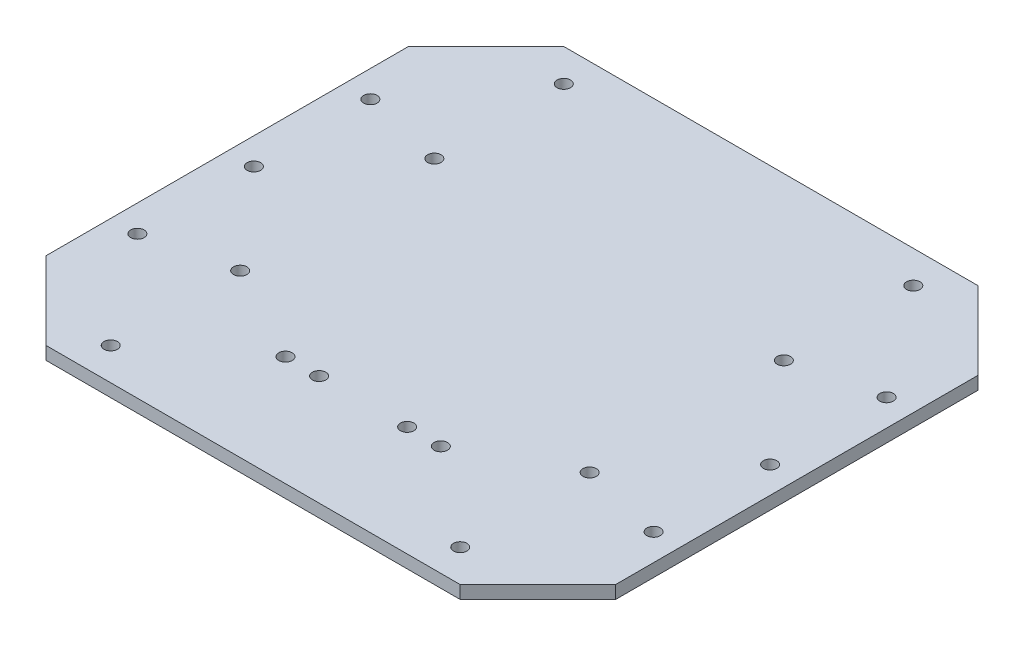
SolidWorks part; units mm, degrees
ref_plane "Front Plane" through (0, 0, 0) normal (0, 0, 1) x (1, 0, 0)
ref_plane "Top Plane" through (0, 0, 0) normal (0, 1, 0) x (1, 0, 0)
ref_plane "Right Plane" through (0, 0, 0) normal (1, 0, 0) x (0, 0, -1)
sketch "Sketch2" plane through (0, 0, 0) normal (0, 1, 0) x (1, 0, 0)
  line L0 (0, 88.9) -> (0, -88.9) construction
  line L1 (-139.7, -88.9) -> (139.7, -88.9) construction
  line L2 (-139.7, -88.9) -> (-139.7, 88.9)
  line L3 (-139.7, 88.9) -> (139.7, 88.9) construction
  line L4 (139.7, -88.9) -> (139.7, 88.9)
  line L5 (-139.7, 0) -> (139.7, 0) construction
  line L6 (-139.7, 88.9) -> (-101.6, 127)
  line L7 (-101.6, 127) -> (101.6, 127)
  line L8 (101.6, 127) -> (139.7, 88.9)
  line L9 (101.6, -127) -> (139.7, -88.9)
  line L10 (-101.6, -127) -> (101.6, -127)
  line L11 (-139.7, -88.9) -> (-101.6, -127)
  circle A11 centre (-21.59, -73.025) radius 3.302
  circle A18 centre (-38.1, -73.025) radius 3.302
  circle A19 centre (38.1, -73.025) radius 3.302
  circle A20 centre (21.59, -73.025) radius 3.302
  dimension "D7" = 45
  dimension "D11" = 21.59
  dimension "D14" = 6.604
  dimension "D15" = 15.875
  dimension "D12" = 6.604
  dimension "D5" = 45
  dimension "D6" = 38.1
  dimension "D1" = 88.9
  dimension "D2" = 177.8
  dimension "D3" = 279.4
  dimension "D4" = 139.7
  dimension "D13" = 38.1
extrude "Boss-Extrude1" add sketch "Sketch2" along normal blind 6.35
sketch "Sketch3" plane through (0, 6.35, 0) normal (0, 1, 0) x (1, 0, 0)
  line L0 (-126.619, 57.15) -> (-126.619, -57.15) construction
  line L1 (-126.619, 0) -> (126.619, 0) construction
  line L2 (126.619, 57.15) -> (126.619, -57.15) construction
  circle A6 centre (-126.619, 57.15) radius 3.302
  circle A7 centre (-126.619, -57.15) radius 3.302
  circle A8 centre (126.619, -57.15) radius 3.302
  circle A9 centre (126.619, 0) radius 3.302
  circle A10 centre (126.619, 57.15) radius 3.302
  circle A11 centre (-126.619, 0) radius 3.302
  point P0 (0, 0)
  dimension "D3" = 6.604
  dimension "D1" = 253.238
  dimension "D2" = 114.3
extrude "Cut-Extrude1" cut sketch "Sketch3" against normal through all
sketch "Sketch4" plane through (0, 0, 0) normal (0, -1, 0) x (1, 0, 0)
  line L0 (85.725, 0) -> (-85.725, 0) construction
  line L1 (-85.725, -47.625) -> (-85.725, 47.625) construction
  line L2 (-85.725, 47.625) -> (-85.725, 111.125) construction
  line L3 (0, 0) -> (0, 39.5223) construction
  line L4 (85.725, -47.625) -> (85.725, 47.625) construction
  line L5 (85.725, 47.625) -> (85.725, 111.125) construction
  line L6 (85.725, -47.625) -> (85.725, -111.125) construction
  line L7 (-85.725, -47.625) -> (-85.725, -111.125) construction
  circle A0 centre (-85.725, 111.125) radius 3.302
  circle A2 centre (-85.725, -111.125) radius 3.302
  circle A3 centre (85.725, -111.125) radius 3.302
  circle A4 centre (85.725, -47.625) radius 3.302
  circle A5 centre (85.725, 47.625) radius 3.302
  circle A6 centre (85.725, 111.125) radius 3.302
  circle A7 centre (-85.725, 47.625) radius 3.302
  circle A8 centre (-85.725, -47.625) radius 3.302
  dimension "D4" = 6.604
  dimension "D1" = 85.725
  dimension "D2" = 47.625
  dimension "D3" = 63.5
extrude "Cut-Extrude2" cut sketch "Sketch4" against normal through all
